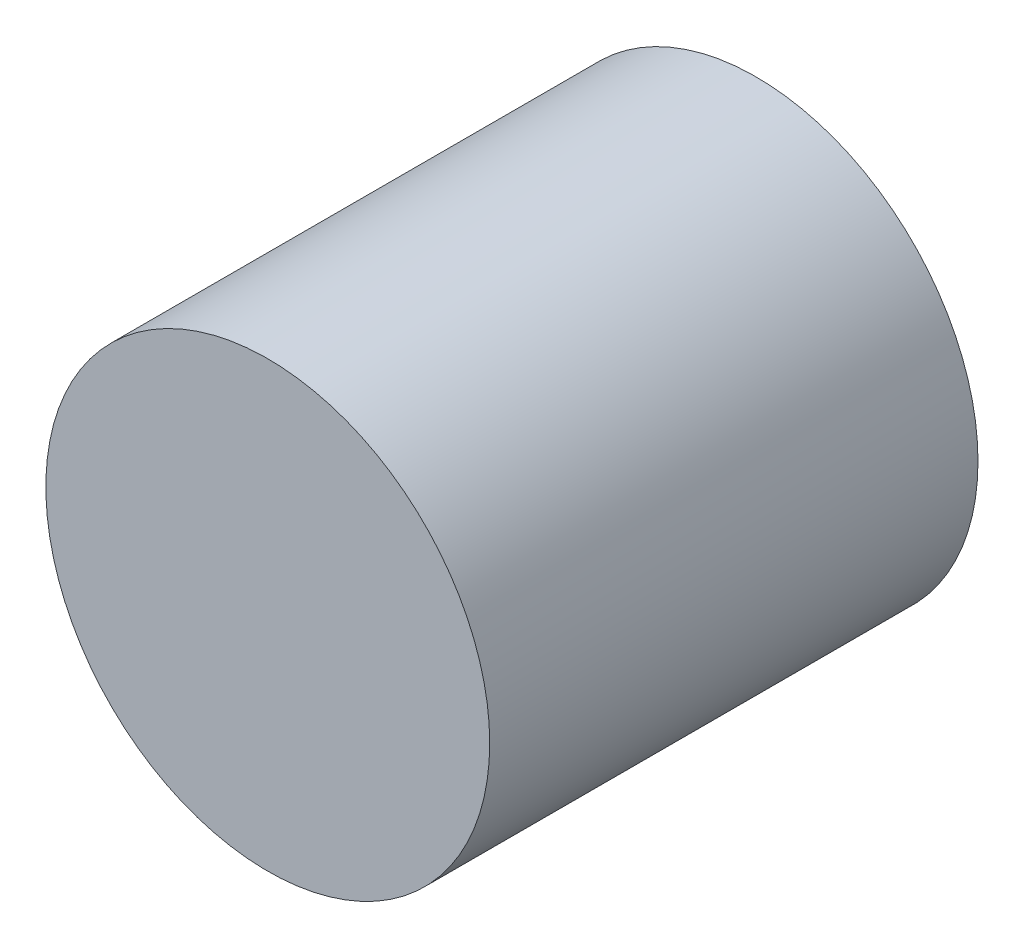
SolidWorks part; units mm, degrees
material "1.0490 (S275N)"
ref_plane "Front Plane" through (0, 0, 0) normal (0, 0, 1) x (1, 0, 0)
ref_plane "Top Plane" through (0, 0, 0) normal (0, 1, 0) x (1, 0, 0)
ref_plane "Right Plane" through (0, 0, 0) normal (1, 0, 0) x (0, 0, -1)
sketch "Sketch1" plane through (0, 0, 0) normal (0, 0, 1) x (1, 0, 0)
  circle A0 centre (0, 0) radius 5
  dimension "D1" = 10
extrude "Boss-Extrude1" add sketch "Sketch1" along normal blind 11
